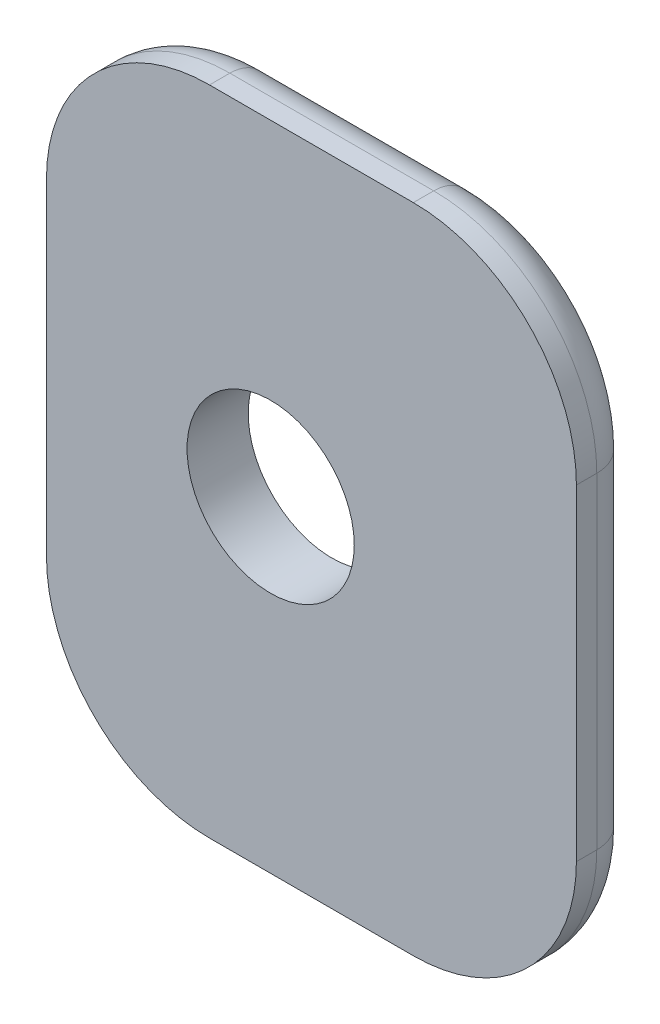
SolidWorks part; units mm, degrees
material "6061-T6 (SS)"
ref_plane "Front Plane" through (0, 0, 0) normal (0, 0, 1) x (1, 0, 0)
ref_plane "Top Plane" through (0, 0, 0) normal (0, 1, 0) x (1, 0, 0)
ref_plane "Right Plane" through (0, 0, 0) normal (1, 0, 0) x (0, 0, -1)
sketch "Sketch1" plane through (0, 0, 0) normal (0, 0, 1) x (1, 0, 0)
  line L0 (0, 0) -> (-11, 0) construction
  line L1 (-11, 16) -> (15, 16)
  line L2 (-11, 16) -> (-11, -16)
  line L3 (-11, -16) -> (15, -16)
  line L4 (15, 16) -> (15, -16)
  circle A0 centre (0, 0) radius 4.1021
  dimension "D1" = 8.2042
  dimension "D2" = 11
  dimension "D3" = 32
  dimension "D4" = 15
extrude "Boss-Extrude1" add sketch "Sketch1" along normal blind 3
fillet "Fillet1" radius 8 4 edges at (15, -16, 1.5) (-11, -16, 1.5) (15, 16, 1.5) (-11, 16, 1.5)
fillet "Fillet2" radius 2 8 edges at (-8.6569, 13.6569, 0) (2, 16, 0) (12.6569, 13.6569, 0) (15, 0, 0) (12.6569, -13.6569, 0) (2, -16, 0) (-8.6569, -13.6569, 0) (-11, 0, 0)
move or copy body "Body-Move/Copy1" [suppressed] bodies to move or copy 101
